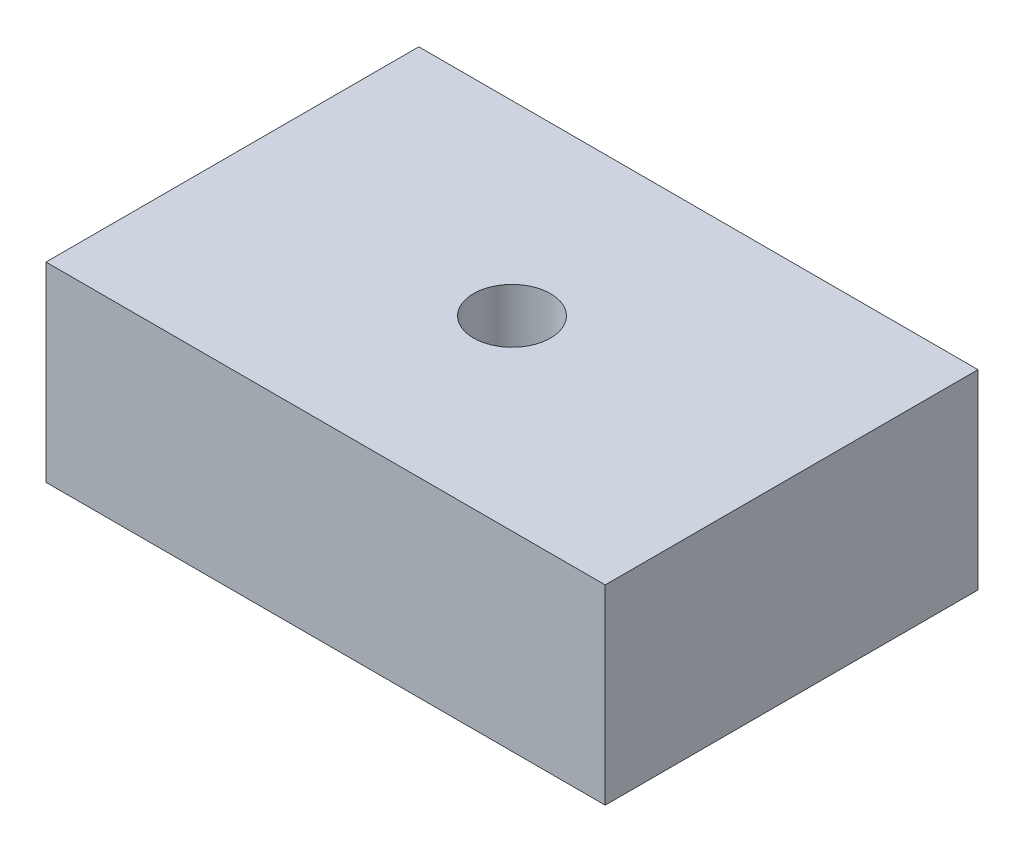
SolidWorks part; units mm, degrees
ref_plane "Front Plane" through (0, 0, 0) normal (0, 0, 1) x (1, 0, 0)
ref_plane "Top Plane" through (0, 0, 0) normal (0, 1, 0) x (1, 0, 0)
ref_plane "Right Plane" through (0, 0, 0) normal (1, 0, 0) x (0, 0, -1)
sketch "Sketch1" plane through (0, 0, 0) normal (0, 1, 0) x (1, 0, 0)
  line L1 (-38.1, 25.4) -> (38.1, 25.4)
  line L2 (-38.1, 25.4) -> (-38.1, -25.4)
  line L3 (-38.1, -25.4) -> (38.1, -25.4)
  line L4 (38.1, 25.4) -> (38.1, -25.4)
  line L5 (-38.1, 25.4) -> (38.1, -25.4) construction
  line L6 (-38.1, -25.4) -> (38.1, 25.4) construction
  circle A0 centre (0, 0) radius 5.25
  dimension "D1" = 50.8
  dimension "D2" = 76.2
extrude "Boss-Extrude1" add sketch "Sketch1" along normal blind 26
